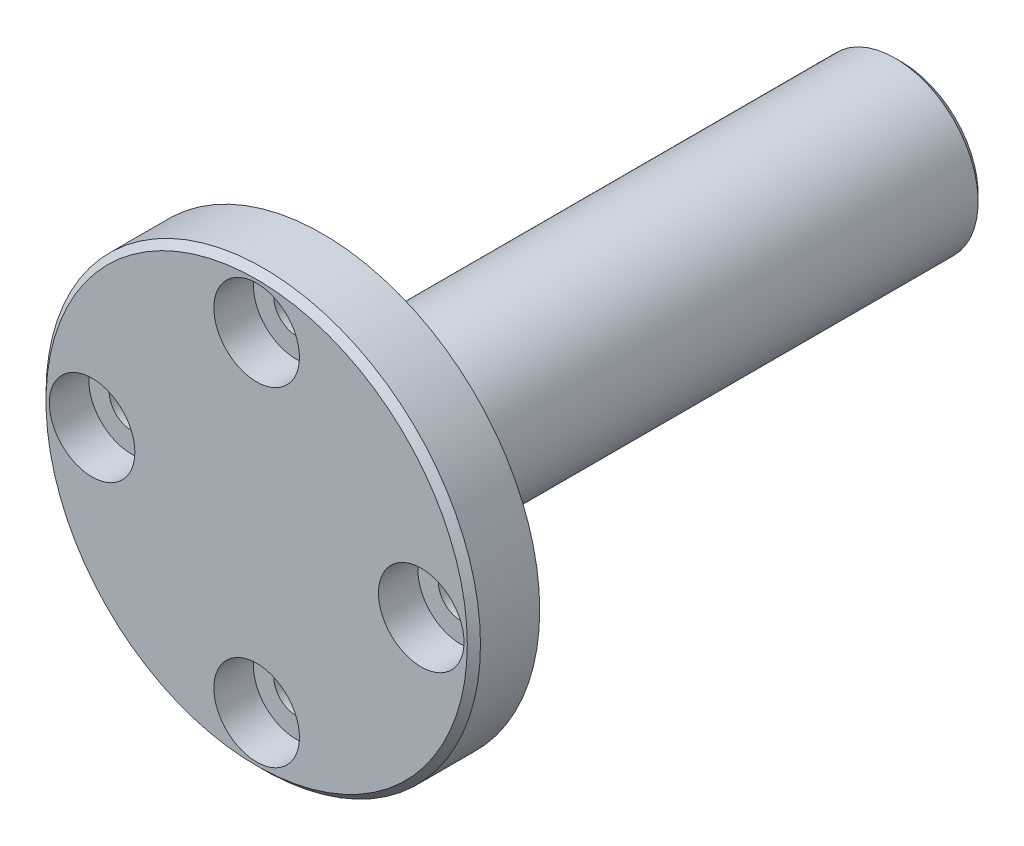
SolidWorks part; units mm, degrees
material "3.1355 (EN-AW 2024)"
ref_plane "Front" through (0, 0, 0) normal (0, 0, 1) x (1, 0, 0)
ref_plane "Top" through (0, 0, 0) normal (0, 1, 0) x (1, 0, 0)
ref_plane "Right" through (0, 0, 0) normal (1, 0, 0) x (0, 0, -1)
sketch "Эскиз2" plane through (0, 0, 0) normal (1, 0, 0) x (0, 0, -1)
  line L0 (0, 0) -> (0, 16.5)
  line L1 (0, 16.5) -> (5, 16.5)
  line L2 (5, 16.5) -> (5, 6.3)
  line L3 (5, 6.3) -> (49, 6.3)
  line L4 (49, 6.3) -> (49, 0)
  line L5 (49, 0) -> (0, 0)
  dimension "D1" = 16.5
  dimension "D2" = 5
  dimension "D3" = 6.3
  dimension "D4" = 44
  dimension "D5" = 49
revolve "Повернуть1" add sketch "Эскиз2" angle 360 about L5
sketch "Эскиз3" plane through (0, 0, 0) normal (0, 0, 1) x (1, 0, 0)
  circle A0 centre (0, 0) radius 12.5 construction
  point P3 (0, 12.5)
  point P7 (12.5, 0)
  point P8 (0, -12.5)
  point P9 (-12.5, 0)
  point P10 (0, 0)
  dimension "D1" = 25
  dimension "D2" = 4
hole_wizard "Цековка для винта с внутренним шестигранником M31" positions "Эскиз5" profile "Эскиз4" counterbore size "M3" standard "Ansi Metric" end condition through all
sketch "Эскиз5" plane through (0, 0, 0) normal (0, 0, 1) x (1, 0, 0)
  point P0 (-12.5, 0)
  point P3 (0, 12.5)
  point P6 (12.5, 0)
  point P9 (0, -12.5)
sketch "Эскиз4" plane through (-12.5, 0, 0) normal (1, 0, 0) x (0, -1, 0)
  line L0 (0, 0) -> (0, 49)
  line L1 (0, 49) -> (1.7, 49)
  line L3 (1.7, 49) -> (1.7, 3)
  line L4 (1.7, 3) -> (3.25, 3)
  line L5 (3.25, 3) -> (3.25, 0)
  line L7 (3.25, 0) -> (0, 0)
  line L11 (0, -6.35) -> (0, 107.95) construction
  dimension "Диаметр сквозного отверстия" = 3.4
  dimension "Глубина сквозного отверстия" = 49
  dimension "Диаметр цековки" = 6.5
  dimension "Глубина цековки" = 3
hole_wizard "Отверстие обработанное метчиком M3x0.51" positions "Эскиз6" profile "Эскиз7" tap size "M3x0.5" standard "Ansi Metric"
sketch "Эскиз6" plane through (2.7067, -7.2328, -49) normal (0, 0, -1) x (-0.6355, -0.7721, 0)
  point P0 (-3.8641, 6.6864)
sketch "Эскиз7" plane through (0, 0, -49) normal (1, 0, 0) x (0, 1, 0)
  line L0 (0, 0) -> (0, 15.7511)
  line L1 (0, 15.7511) -> (1.25, 15)
  line L2 (1.25, 15) -> (1.25, 0)
  line L3 (1.25, 0) -> (0, 0)
  line L4 (0, 15.7511) -> (-1.25, 15) construction
  line L5 (0, -6.35) -> (0, 107.95) construction
  dimension "Диаметр сверла" = 2.5
  dimension "Глубина сверла" = 15
  dimension "Угол заточки сверла" = 118
cosmetic thread "Отверстие резьбы1" parameters "D1"=13, "D2"=3
chamfer "Фаска1" distance 0.5 angle 45 2 edges at (-6.3, 0, -49) (-16.5, 0, 0)
